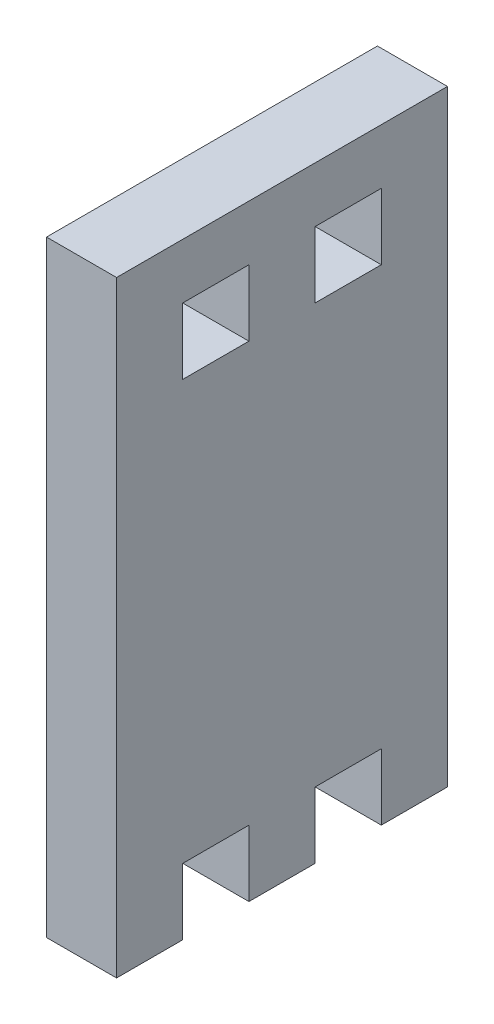
SolidWorks part; units mm, degrees
ref_plane "Front" through (0, 0, 0) normal (0, 0, 1) x (1, 0, 0)
ref_plane "Top" through (0, 0, 0) normal (0, 1, 0) x (1, 0, 0)
ref_plane "Right" through (0, 0, 0) normal (1, 0, 0) x (0, 0, -1)
sketch "Sketch1" plane through (0, 0, 0) normal (1, 0, 0) x (0, 0, -1)
  line L0 (-18.5982, 0) -> (21.6004, 0) construction
  line L1 (-15, 27.5) -> (15, 27.5)
  line L2 (-15, 27.5) -> (-15, -27.5)
  line L3 (-15, -27.5) -> (-9, -27.5)
  line L4 (15, 27.5) -> (15, -27.5)
  line L5 (-15, 27.5) -> (15, -27.5) construction
  line L6 (-15, -27.5) -> (15, 27.5) construction
  line L7 (-9, 22.5) -> (-3, 22.5)
  line L8 (-9, 22.5) -> (-9, 16.5)
  line L9 (-9, 16.5) -> (-3, 16.5)
  line L10 (-3, 22.5) -> (-3, 16.5)
  line L11 (-9, 22.5) -> (-3, 16.5) construction
  line L12 (-9, 16.5) -> (-3, 22.5) construction
  line L17 (0, 29.142) -> (0, -28.9726) construction
  line L22 (9, 22.5) -> (9, 16.5)
  line L23 (9, 22.5) -> (3, 22.5)
  line L24 (3, 22.5) -> (3, 16.5)
  line L25 (9, 16.5) -> (3, 16.5)
  line L27 (-3, -21.5) -> (-9, -21.5)
  line L28 (-3, -21.5) -> (-3, -27.5)
  line L30 (-9, -21.5) -> (-9, -27.5)
  line L31 (-3, -21.5) -> (-9, -27.5) construction
  line L32 (-3, -27.5) -> (-9, -21.5) construction
  line L34 (9, -21.5) -> (9, -27.5)
  line L35 (3, -21.5) -> (9, -21.5)
  line L36 (3, -21.5) -> (3, -27.5)
  line L37 (9, -27.5) -> (15, -27.5)
  line L38 (-3, -27.5) -> (3, -27.5)
  point P0 (0, 0)
  point P6 (-6, 19.5)
  point P15 (-6, 22.5)
  point P16 (-6, -24.5)
  dimension "D1" = 30
  dimension "D2" = 55
  dimension "D4" = 6
  dimension "D5" = 6
  dimension "D3" = 3
  dimension "D6" = 5
extrude "Boss-Extrude1" add sketch "Sketch1" along normal blind 6.35 contours L28 L38 L36 L35 L34 L37 L4 L1 L2 L3 L30 L27 L22 L25 L24 L23 L7 L10 L9 L8
equation "\"D2@Sketch1\"=50+\"D6@Sketch1\""
